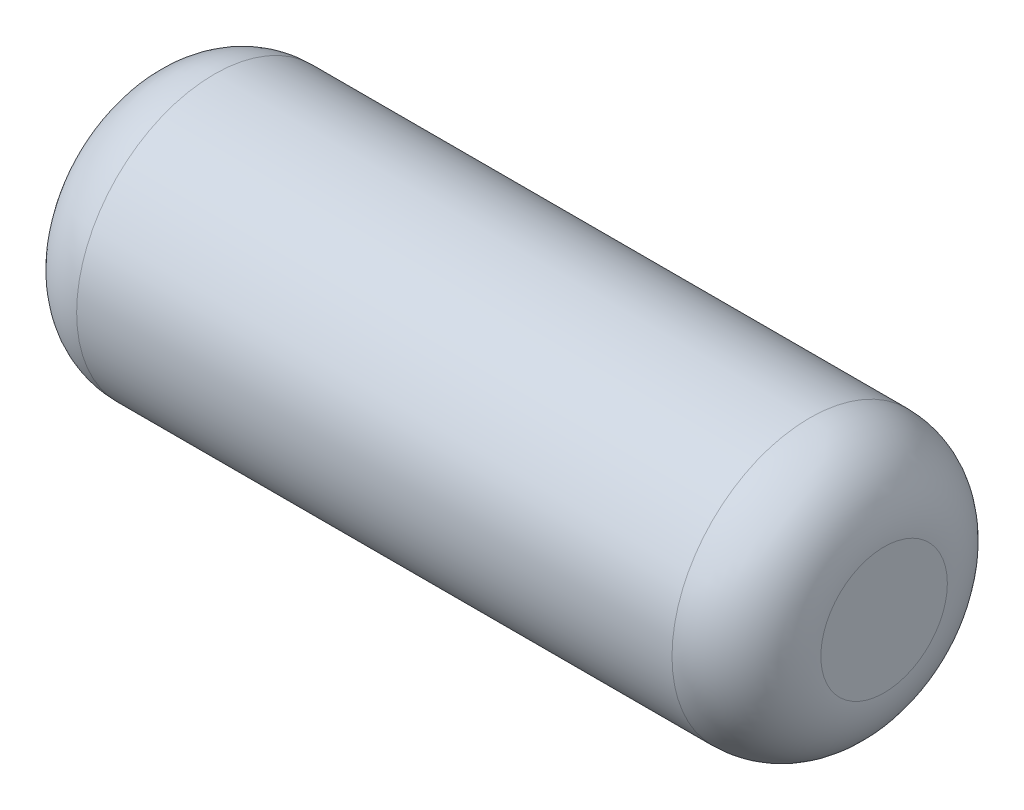
SolidWorks part; units mm, degrees
material "Plain Carbon Steel"
ref_plane "Front Plane" through (0, 0, 0) normal (0, 0, 1) x (1, 0, 0)
ref_plane "Top Plane" through (0, 0, 0) normal (0, 1, 0) x (1, 0, 0)
ref_plane "Right Plane" through (0, 0, 0) normal (1, 0, 0) x (0, 0, -1)
other "Configuration Table"
sketch "Sketch1" plane through (0, 0, 0) normal (1, 0, 0) x (0, 0, -1)
  circle A0 centre (0, 0) radius 4.699
  dimension "D1" = 9.398
extrude "Boss-Extrude1" add sketch "Sketch1" along normal mid plane 25.4
fillet "Fillet1" radius 2.54 2 edges at (-12.7, 0, -4.699) (12.7, 0, -4.699)
